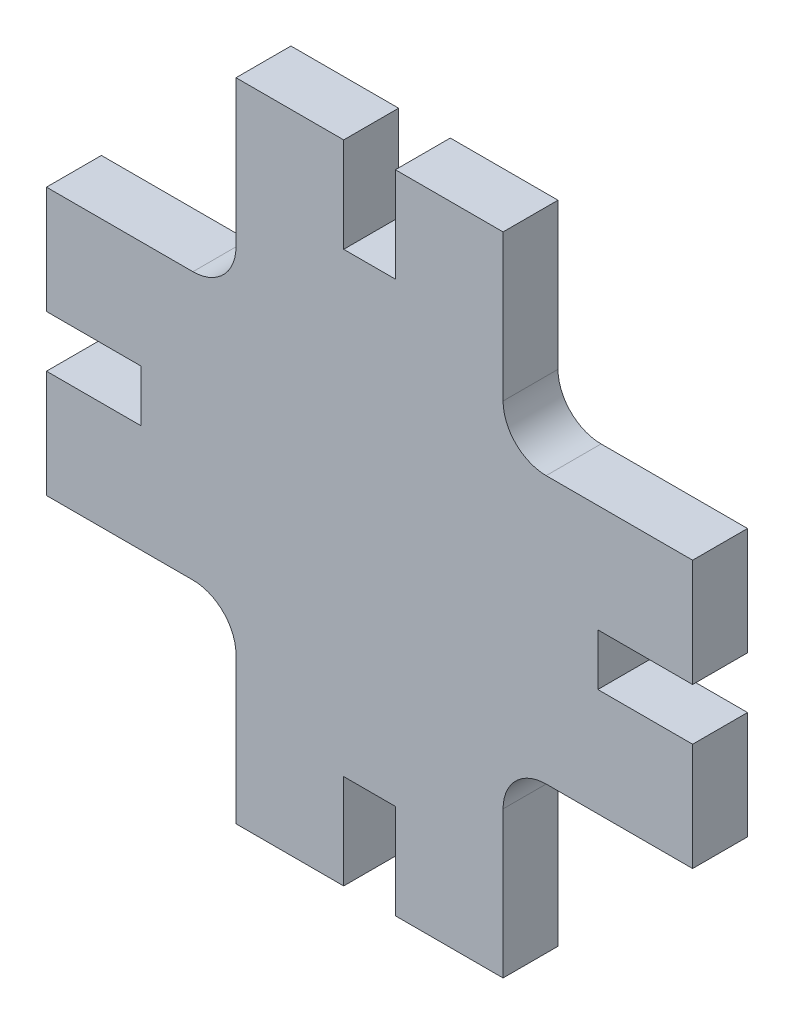
SolidWorks part; units mm, degrees
material "Balsa"
ref_plane "Alzado" through (0, 0, 0) normal (0, 0, 1) x (1, 0, 0)
ref_plane "Planta" through (0, 0, 0) normal (0, 1, 0) x (1, 0, 0)
ref_plane "Vista lateral" through (0, 0, 0) normal (1, 0, 0) x (0, 0, -1)
sketch "Croquis1" plane through (0, 0, 0) normal (0, 0, 1) x (1, 0, 0)
  line L0 (0, 0) -> (10, 0)
  line L1 (10, 0) -> (10, 8.8)
  line L2 (10, 8.8) -> (14.8, 8.8)
  line L3 (14.8, 8.8) -> (14.8, 0)
  line L4 (14.8, 0) -> (24.8, 0)
  line L5 (24.8, 0) -> (24.8, 13.6)
  line L6 (0, 0) -> (0, 13.6)
  line L7 (-4, 17.6) -> (-17.6, 17.6)
  line L8 (-17.6, 17.6) -> (-17.6, 27.6)
  line L9 (-17.6, 27.6) -> (-8.8, 27.6)
  line L10 (-8.8, 27.6) -> (-8.8, 32.4)
  line L11 (-8.8, 32.4) -> (-17.6, 32.4)
  line L12 (-17.6, 32.4) -> (-17.6, 42.4)
  line L13 (-17.6, 42.4) -> (-4, 42.4)
  line L14 (0, 46.4) -> (0, 60)
  line L15 (0, 60) -> (10, 60)
  line L16 (10, 60) -> (10, 51.2)
  line L17 (10, 51.2) -> (14.8, 51.2)
  line L18 (14.8, 51.2) -> (14.8, 60)
  line L19 (14.8, 60) -> (24.8, 60)
  line L20 (24.8, 60) -> (24.8, 46.4)
  line L21 (28.8, 42.4) -> (42.4, 42.4)
  line L22 (42.4, 42.4) -> (42.4, 32.4)
  line L23 (42.4, 32.4) -> (33.6, 32.4)
  line L24 (33.6, 32.4) -> (33.6, 27.6)
  line L25 (33.6, 27.6) -> (42.4, 27.6)
  line L26 (42.4, 27.6) -> (42.4, 17.6)
  line L27 (42.4, 17.6) -> (28.8, 17.6)
  line L28 (12.4, 8.8) -> (12.4, 30) construction
  line L29 (12.4, 30) -> (12.4, 51.2) construction
  line L30 (12.4, 51.2) -> (12.4, 30) construction
  line L31 (33.6, 30) -> (12.4, 30) construction
  line L32 (12.4, 30) -> (-8.8, 30) construction
  line L33 (-1.1716, 16.4284) -> (25.9716, 43.5716) construction
  line L34 (-1.1716, 43.5716) -> (25.9716, 16.4284) construction
  arc A1 (-4, 17.6) -> (0, 13.6) centre (-4, 13.6) cw
  arc A2 (-4, 42.4) -> (0, 46.4) centre (-4, 46.4) ccw
  arc A3 (24.8, 46.4) -> (28.8, 42.4) centre (28.8, 46.4) ccw
  arc A4 (24.8, 13.6) -> (28.8, 17.6) centre (28.8, 13.6) cw
  point P35 (33.6, 30)
  point P39 (12.4, 30)
  point P42 (-8.8, 30)
extrude "Saliente-Extruir1" add sketch "Croquis1" along normal blind 5.1
equation "\"Ranura\"=4.8"
equation "\"D5@Croquis1\"=\"Ranura\""
equation "\"D4@Croquis1\"=\"D5@Croquis1\"+4"
